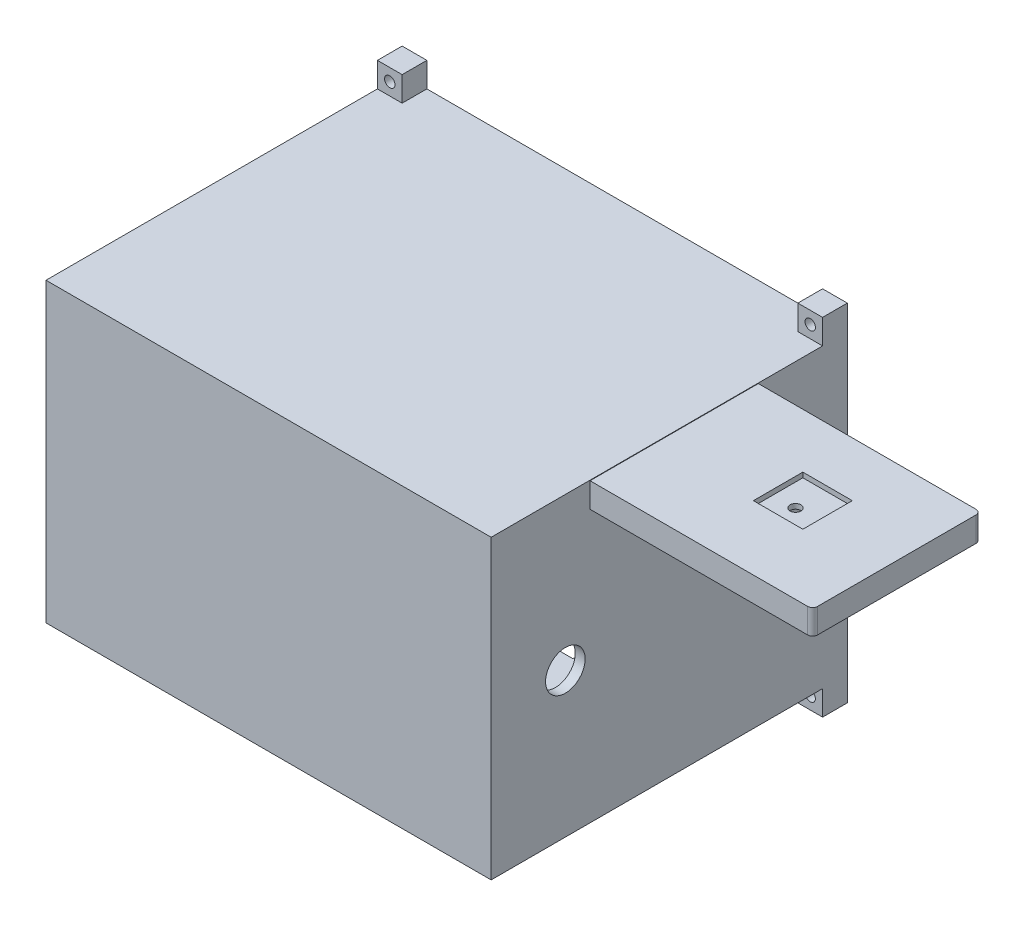
SolidWorks part; units mm, degrees
ref_plane "前基準面" through (0, 0, 0) normal (0, 0, 1) x (1, 0, 0)
ref_plane "上基準面" through (0, 0, 0) normal (0, 1, 0) x (1, 0, 0)
ref_plane "右基準面" through (0, 0, 0) normal (1, 0, 0) x (0, 0, -1)
sketch "草圖1" plane through (0, 0, 0) normal (0, 0, 1) x (1, 0, 0)
  line L0 (-75.5089, 25.5899) -> (59.4911, 25.5899)
  line L4 (-75.5089, -4.4101) -> (59.4911, -4.4101) construction
  line L5 (-75.5089, 25.5899) -> (-75.5089, -34.4101)
  line L6 (59.4911, 25.5899) -> (59.4911, -34.4101)
  line L7 (-75.5089, -34.4101) -> (59.4911, -34.4101)
  dimension "D1" = 135
  dimension "D2" = 60
extrude "填料-伸長1" add sketch "草圖1" along normal blind 70
sketch "草圖5" plane through (0, -34.4101, 0) normal (0, -1, 0) x (1, 0, 0)
  line L0 (14.4911, 70) -> (14.4911, 0)
  line L1 (-75.5089, 70) -> (59.4911, 70) construction
  line L2 (-75.5089, 0) -> (59.4911, 0) construction
  line L3 (14.4911, 0) -> (59.4911, 0)
  line L4 (59.4911, 0) -> (59.4911, 70)
  line L5 (59.4911, 70) -> (14.4911, 70)
  dimension "D1" = 45
sketch "草圖6" plane through (0, 25.5899, 0) normal (0, 1, 0) x (1, 0, 0)
  line L0 (14.4911, 0) -> (14.4911, -70)
  line L1 (14.4911, -70) -> (59.4911, -70)
  line L2 (59.4911, -70) -> (59.4911, 0)
  line L3 (59.4911, 0) -> (14.4911, 0)
extrude "除料-伸長1" cut sketch "草圖6" against normal blind 0.1
extrude "除料-伸長2" cut sketch "草圖5" against normal blind 54.9
sketch "草圖7" plane through (0, 0, 0) normal (0, 0, 1) x (1, 0, 0)
  line L0 (-75.5089, -34.4101) -> (14.4911, -34.4101) construction
  line L1 (-75.5089, 25.5899) -> (-75.5089, -34.4101) construction
  line L3 (-70.5089, -29.4101) -> (-70.5089, 20.5899)
  line L4 (-70.5089, 20.5899) -> (9.4911, 20.5899)
  line L5 (9.4911, 20.5899) -> (9.4911, -29.4101)
  line L6 (-70.5089, -29.4101) -> (9.4911, -29.4101)
  line L7 (14.4911, 25.5899) -> (-75.5089, 25.5899) construction
  line L8 (14.4911, 20.4899) -> (14.4911, -34.4101) construction
  point P11 (9.4911, -4.4101)
  point P12 (-70.5089, -4.4101)
  dimension "D1" = 5
  dimension "D2" = 5
  dimension "D3" = 5
  dimension "D4" = 5
  dimension "D5" = 80
  dimension "D6" = 50
extrude "除料-伸長3" cut sketch "草圖7" along normal blind 75
sketch "草圖8" plane through (0, 0, 0) normal (0, 0, -1) x (-1, 0, 0)
  line L2 (75.5089, 25.5899) -> (75.5089, -34.4101) construction
  line L3 (-13.4911, 22.5899) -> (-13.4911, -31.4101)
  line L4 (-11.4911, 24.5899) -> (72.5089, 24.5899)
  line L5 (74.5089, 22.5899) -> (74.5089, -31.4101)
  line L7 (71.5089, -28.4101) -> (71.5089, 19.5899)
  line L8 (69.5089, 21.5899) -> (-8.4911, 21.5899)
  line L9 (-10.4911, 19.5899) -> (-10.4911, -28.4101)
  line L11 (-14.4911, 25.5899) -> (75.5089, 25.5899) construction
  line L12 (-14.4911, 25.4899) -> (-14.4911, 25.5899) construction
  line L13 (69.5089, -30.4101) -> (-8.4911, -30.4101)
  line L14 (-11.4911, -33.4101) -> (72.5089, -33.4101)
  line L15 (75.5089, -34.4101) -> (-14.4911, -34.4101) construction
  arc A0 (-8.4911, 21.5899) -> (-10.4911, 19.5899) centre (-8.4911, 19.5899) ccw
  arc A1 (-13.4911, 22.5899) -> (-11.4911, 24.5899) centre (-11.4911, 22.5899) cw
  arc A2 (71.5089, 19.5899) -> (69.5089, 21.5899) centre (69.5089, 19.5899) ccw
  arc A3 (72.5089, 24.5899) -> (74.5089, 22.5899) centre (72.5089, 22.5899) cw
  arc A4 (-11.4911, -33.4101) -> (-13.4911, -31.4101) centre (-11.4911, -31.4101) cw
  arc A5 (-8.4911, -30.4101) -> (-10.4911, -28.4101) centre (-8.4911, -28.4101) cw
  arc A6 (72.5089, -33.4101) -> (74.5089, -31.4101) centre (72.5089, -31.4101) ccw
  arc A7 (69.5089, -30.4101) -> (71.5089, -28.4101) centre (69.5089, -28.4101) ccw
  dimension "D9" = 2
  dimension "D10" = 2
  dimension "D11" = 2
  dimension "D12" = 2
  dimension "D13" = 2
  dimension "D1" = 3
  dimension "D2" = 3
  dimension "D3" = 3
  dimension "D4" = 1
  dimension "D5" = 1
  dimension "D6" = 1
  dimension "D7" = 3
  dimension "D8" = 1
extrude "除料-伸長4" cut sketch "草圖8" against normal blind 6
ref_plane "平面1" through (14.4911, 0, 0) normal (1, 0, 0) x (0, 0, -1)
ref_plane "平面2" through (0, -34.4101, 0) normal (0, -1, 0) x (-1, 0, 0)
sketch "草圖10" plane through (0, -34.4101, 0) normal (0, -1, 0) x (-1, 0, 0)
  line L0 (75.5089, 0) -> (-14.4911, 0) construction
  line L1 (14.0089, -12) -> (35.5089, -12)
  line L2 (14.0089, -12) -> (14.0089, -27)
  line L3 (14.0089, -27) -> (35.5089, -27)
  line L4 (35.5089, -12) -> (35.5089, -27)
  line L5 (75.5089, -70) -> (75.5089, 0) construction
  point P6 (24.7589, -12)
  dimension "D1" = 21.5
  dimension "D2" = 15
  dimension "D3" = 12
  dimension "D4" = 40
extrude "除料-伸長6" cut sketch "草圖10" against normal blind 10
sketch "草圖12" plane through (14.4911, 0, 0) normal (1, 0, 0) x (0, 0, -1)
  line L0 (-35, 25.5899) -> (-35, -34.4101) construction
  line L1 (0, 25.5899) -> (-70, 25.5899) construction
  line L2 (-70, -34.4101) -> (0, -34.4101) construction
  line L5 (-52.0113, 30.9392) -> (-52.0113, 0.5899)
  line L7 (-70.9175, 30.9392) -> (-52.0113, 30.9392)
  line L9 (-17.9887, 0.5899) -> (0.9175, 0.5899)
  line L10 (0.9175, 0.5899) -> (0.9175, 30.9392)
  line L11 (0.9175, 30.9392) -> (-17.9887, 30.9392)
  line L12 (-17.9887, 30.9392) -> (-17.9887, 0.5899)
  line L13 (-70.9175, 0.5899) -> (-70.9175, 30.9392)
  line L14 (-52.0113, 0.5899) -> (-70.9175, 0.5899)
  dimension "D2" = 25
extrude "除料-伸長7" cut sketch "草圖12" along normal blind 50
ref_plane "平面3" through (0, 20.4899, 0) normal (0, -1, 0) x (-1, 0, 0)
sketch "草圖14" plane through (0, 20.4899, 0) normal (0, -1, 0) x (-1, 0, 0)
  line L4 (-59.4911, -35) -> (-70.9929, -35) construction
  line L5 (-59.4911, -17.9887) -> (-59.4911, -52.0113) construction
  line L6 (-38.1261, -30.0802) -> (-22.0179, -33)
  line L7 (-38.1261, -39.9198) -> (-22.0179, -37)
  line L8 (-39.0179, -40) -> (-39.0179, -45.1799) construction
  line L9 (-39.9097, -39.9198) -> (-56.0179, -37)
  line L10 (-39.9097, -30.0802) -> (-56.0179, -33)
  line L11 (-49.9929, -35) -> (-38.9929, -35) construction
  line L12 (-20.0179, -35) -> (-28.4331, -35) construction
  line L13 (-14.4911, -52.0113) -> (-14.4911, -17.9887) construction
  arc A2 (-39.9097, -39.9198) -> (-38.1261, -39.9198) centre (-39.0179, -35) ccw
  arc A3 (-22.0179, -37) -> (-22.0179, -33) centre (-22.0179, -35) ccw
  arc A5 (-56.0179, -37) -> (-56.0179, -33) centre (-56.0179, -35) cw
  arc A6 (-38.1261, -30.0802) -> (-39.9097, -30.0802) centre (-39.0179, -35) ccw
  point P21 (-58.0179, -35)
  dimension "D1" = 10
  dimension "D2" = 4
  dimension "D3" = 1.4732
  dimension "D4" = 5.5268
extrude "除料-伸長8" cut sketch "草圖14" against normal blind 3
ref_plane "平面4" through (0, 25.4899, 0) normal (0, 1, 0) x (1, 0, 0)
sketch "草圖15" plane through (0, 25.4899, 0) normal (0, 1, 0) x (1, 0, 0)
  line L0 (14.4911, -17.9887) -> (14.4911, -52.0113) construction
  line L1 (34.4911, -28.9887) -> (44.4911, -28.9887)
  line L2 (34.4911, -28.9887) -> (34.4911, -38.9887)
  line L3 (34.4911, -38.9887) -> (44.4911, -38.9887)
  line L4 (44.4911, -28.9887) -> (44.4911, -38.9887)
  line L5 (59.4911, -17.9887) -> (14.4911, -17.9887) construction
  dimension "D1" = 10
  dimension "D2" = 10
  dimension "D3" = 20
  dimension "D4" = 11
extrude "除料-伸長9" cut sketch "草圖15" against normal blind 1
sketch "草圖17" plane through (0, 20.4899, 0) normal (0, -1, 0) x (-1, 0, 0)
  line L0 (-58.0179, -35) -> (-20.0179, -35) construction
  line L1 (-39.0179, -40) -> (-39.0179, -30) construction
  arc A0 (-56.0179, -33) -> (-56.0179, -37) centre (-56.0179, -35) ccw construction
  arc A1 (-22.0179, -37) -> (-22.0179, -33) centre (-22.0179, -35) ccw construction
  arc A2 (-39.9097, -39.9198) -> (-38.1261, -39.9198) centre (-39.0179, -35) ccw construction
  arc A3 (-38.1261, -30.0802) -> (-39.9097, -30.0802) centre (-39.0179, -35) ccw construction
  circle A4 centre (-39.0179, -35) radius 1.0953
extrude "除料-伸長11" cut sketch "草圖17" against normal blind 7
sketch "草圖18" plane through (0, 0, 0) normal (0, 0, 1) x (1, 0, 0)
  line L0 (-75.5089, -4.4101) -> (9.4911, -4.4101) construction
  line L1 (14.4911, 25.5899) -> (9.4911, 25.5899)
  line L2 (14.4911, 25.5899) -> (14.4911, 30.5899)
  line L3 (14.4911, 25.5899) -> (-75.5089, 25.5899) construction
  line L4 (-30.5089, 25.5899) -> (-30.5089, -34.4101) construction
  line L5 (-38.5, -34.4101) -> (38.5, -34.4101) construction
  line L6 (14.4911, 30.5899) -> (9.4911, 30.5899)
  line L11 (9.4911, 25.5899) -> (9.4911, 30.5899)
  line L12 (-75.5089, 25.5899) -> (-70.5089, 25.5899)
  line L17 (-75.5089, -34.4101) -> (-70.5089, -34.4101)
  line L18 (-75.5089, -34.4101) -> (-75.5089, -39.4101)
  line L19 (-75.5089, -39.4101) -> (-70.5089, -39.4101)
  line L20 (-70.5089, -34.4101) -> (-70.5089, -39.4101)
  line L21 (14.4911, -34.4101) -> (9.4911, -34.4101)
  line L22 (9.4911, -34.4101) -> (9.4911, -39.4101)
  line L23 (14.4911, -39.4101) -> (9.4911, -39.4101)
  line L24 (14.4911, -34.4101) -> (14.4911, -39.4101)
  line L25 (-75.5089, 25.5899) -> (-75.5089, -34.4101) construction
  line L26 (9.4911, -29.4101) -> (9.4911, 20.5899) construction
  line L27 (-75.5089, 25.5899) -> (-75.5089, 30.5899)
  line L28 (-75.5089, 30.5899) -> (-70.5089, 30.5899)
  line L29 (-70.5089, 25.5899) -> (-70.5089, 30.5899)
  circle A2 centre (-73.0089, -36.9101) radius 1.05
  circle A3 centre (11.9911, -36.9101) radius 1.05
  circle A4 centre (11.9911, 28.0899) radius 1.05
  circle A5 centre (-73.0089, 28.0899) radius 1.05
  dimension "D3" = 2.1
  dimension "D1" = 2.1
  dimension "D2" = 2.1
  dimension "D4" = 2.1
extrude "填料-伸長2" add sketch "草圖18" along normal blind 5
ref_plane "平面5" through (0, 0, 70) normal (0, 0, 1) x (1, 0, 0)
sketch "草圖19" plane through (0, 0, 70) normal (0, 0, 1) x (1, 0, 0)
  line L0 (14.4911, -43.147) -> (14.4911, 43.147) construction
  line L1 (-75.5089, 25.5899) -> (14.4911, 25.5899)
  line L2 (-75.5089, 25.5899) -> (-75.5089, -34.4101)
  line L3 (-75.5089, -34.4101) -> (14.4911, -34.4101)
  line L4 (14.4911, 25.5899) -> (14.4911, -34.4101)
  dimension "D1" = 60
  dimension "D2" = 90
extrude "填料-伸長3" add sketch "草圖19" along normal blind 2
sketch "草圖20" plane through (14.4911, 0, 0) normal (1, 0, 0) x (0, 0, -1)
  line L0 (-72, -4.4101) -> (0, -4.4101) construction
  line L1 (-72, -34.4101) -> (-72, 25.5899) construction
  line L2 (0, -39.4101) -> (0, 30.5899) construction
  line L3 (-36, -4.4101) -> (-36, -34.9619) construction
  circle A1 centre (-15, -5.2142) radius 4
  circle A2 centre (-57, -5.2142) radius 4
  dimension "D1" = 8
  dimension "D5" = 15
extrude "除料-伸長12" cut sketch "草圖20" against normal blind 10
ref_plane "平面6" through (0, 0, 7) normal (0, 0, -1) x (-1, 0, 0)
sketch "草圖21" plane through (0, 0, 7) normal (0, 0, -1) x (-1, 0, 0)
  line L0 (-13.4911, -4.4101) -> (75.5089, -4.4101) construction
  line L1 (-13.4911, 22.5899) -> (-13.4911, -31.4101) construction
  line L2 (75.5089, 30.5899) -> (75.5089, -39.4101) construction
  line L3 (30.5089, 25.5899) -> (30.5089, -34.4101) construction
  line L4 (-9.4911, 25.5899) -> (70.5089, 25.5899) construction
  line L5 (-39.6, -34.4101) -> (39.6, -34.4101) construction
  line L6 (-14.4911, 43.147) -> (-14.4911, -43.147) construction
  line L7 (-12.4911, 23.5899) -> (73.5089, 23.5899)
  line L8 (-12.4911, 23.5899) -> (-12.4911, -32.4101)
  line L9 (-12.4911, -32.4101) -> (73.5089, -32.4101)
  line L10 (73.5089, 23.5899) -> (73.5089, -32.4101)
  dimension "D1" = 2
  dimension "D2" = 2
  dimension "D3" = 2
  dimension "D4" = 2
extrude "除料-伸長13" cut sketch "草圖21" against normal blind 63
fillet "圓角3" radius 1 1 edges at (59.4911, 22.9899, 17.9887)
fillet "圓角4" radius 1 1 edges at (59.4911, 22.9899, 52.0113)
